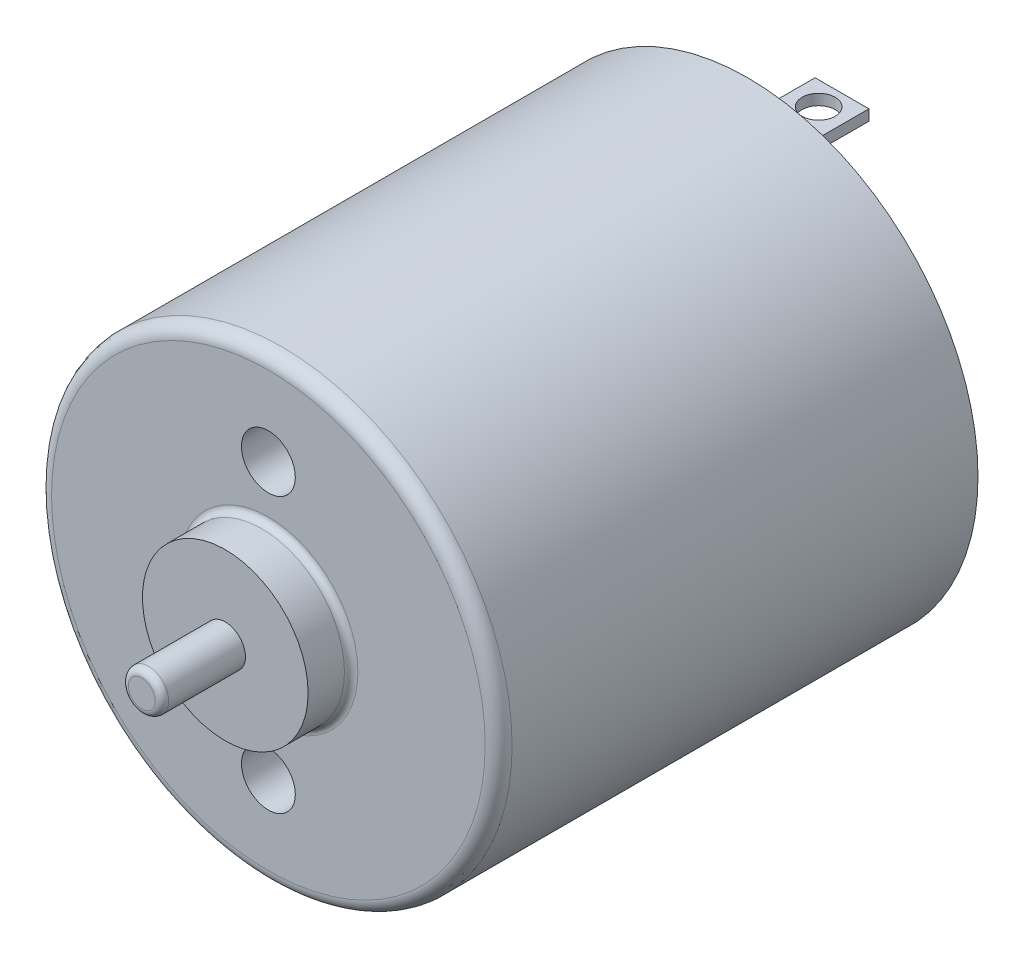
SolidWorks part; units mm, degrees
ref_plane "Front Plane" through (0, 0, 0) normal (0, 0, 1) x (1, 0, 0)
ref_plane "Top Plane" through (0, 0, 0) normal (0, 1, 0) x (1, 0, 0)
ref_plane "Right Plane" through (0, 0, 0) normal (1, 0, 0) x (0, 0, -1)
sketch "Sketch1" plane through (0, 0, 0) normal (0, 0, 1) x (1, 0, 0)
  circle A0 centre (0, 0) radius 8.55
  dimension "D1" = 17.1
extrude "Boss-Extrude1" add sketch "Sketch1" along normal blind 17.8
sketch "Sketch2" plane through (0, 0, 17.8) normal (0, 0, 1) x (1, 0, 0)
  circle A0 centre (0, 0) radius 3.075
  dimension "D1" = 6.15
extrude "Boss-Extrude2" add sketch "Sketch2" along normal blind 1.6
sketch "Sketch3" plane through (0, 0, 19.4) normal (0, 0, 1) x (1, 0, 0)
  circle A0 centre (0, 0) radius 0.75
  dimension "D1" = 1.5
extrude "Boss-Extrude3" add sketch "Sketch3" along normal offset from surface (3.1 mm away) 4.7 up to face at (3.075, 0, 17.8) offset beyond the face yes
sketch "Sketch4" plane through (0, 0, 17.8) normal (0, 0, 1) x (1, 0, 0)
  line L0 (0, 5.1) -> (0, -5.1) construction
  circle A0 centre (0, 5.1) radius 1
  circle A1 centre (0, -5.1) radius 1
  point P4 (0, 0)
  dimension "D2" = 2
  dimension "D1" = 10.2
extrude "Cut-Extrude1" cut sketch "Sketch4" against normal blind 2
sketch "Sketch5" plane through (0, 0, 0) normal (0, 0, -1) x (-1, 0, 0)
  circle A0 centre (0, 0) radius 2.35
  dimension "D1" = 4.7
extrude "Boss-Extrude4" add sketch "Sketch5" along normal blind 2.16
sketch "Sketch6" plane through (0, 0, 0) normal (0, 0, -1) x (-1, 0, 0)
  line L0 (0, 6.1) -> (0, -6.1) construction
  line L1 (-1, 5.9) -> (1, 5.9)
  line L2 (-1, 5.9) -> (-1, 6.3)
  line L3 (-1, 6.3) -> (1, 6.3)
  line L4 (1, 5.9) -> (1, 6.3)
  line L5 (-1, 5.9) -> (1, 6.3) construction
  line L6 (-1, 6.3) -> (1, 5.9) construction
  line L7 (-1, -6.3) -> (1, -6.3)
  line L8 (-1, -6.3) -> (-1, -5.9)
  line L9 (-1, -5.9) -> (1, -5.9)
  line L10 (1, -6.3) -> (1, -5.9)
  line L11 (-1, -6.3) -> (1, -5.9) construction
  line L12 (-1, -5.9) -> (1, -6.3) construction
  point P0 (0, 6.1)
  point P5 (0, -6.1)
  point P12 (0, 0)
  dimension "D1" = 11.8
  dimension "D2" = 2
  dimension "D3" = 0.4
  dimension "D4" = 0.4
extrude "Boss-Extrude5" add sketch "Sketch6" along normal blind 3.5
fillet "Fillet1" radius 0.5 1 edges at (8.55, 0, 17.8)
fillet "Fillet2" radius 0.25 1 edges at (3.075, 0, 17.8)
fillet "Fillet3" radius 0.5 1 edges at (-2.35, 0, -2.16)
sketch "Sketch7" plane through (0, 0, 0) normal (0, 0, -1) x (-1, 0, 0)
  line L0 (1, 5.9) -> (1, 6.3) construction
  line L1 (1, 6.3) -> (-1, 6.3) construction
  line L2 (-1, 6.3) -> (-1, 5.9) construction
  line L3 (-1, 5.9) -> (1, 5.9) construction
  line L4 (1, -6.3) -> (1, -5.9) construction
  line L5 (1, -5.9) -> (-1, -5.9) construction
  line L6 (-1, -5.9) -> (-1, -6.3) construction
  line L7 (-1, -6.3) -> (1, -6.3) construction
  line L8 (1, 5.9) -> (1, 6.3)
  line L9 (1, 6.3) -> (-1, 6.3)
  line L10 (-1, 6.3) -> (-1, 5.9)
  line L11 (-1, 5.9) -> (1, 5.9)
  line L12 (1, -6.3) -> (1, -5.9)
  line L13 (1, -5.9) -> (-1, -5.9)
  line L14 (-1, -5.9) -> (-1, -6.3)
  line L15 (-1, -6.3) -> (1, -6.3)
  circle A0 centre (0, 0) radius 2.35 construction
  circle A1 centre (0, 0) radius 8.55
  circle A2 centre (0, 0) radius 8.55 construction
  circle A3 centre (0, 0) radius 2.35
  circle A4 centre (0, 0) radius 8.3
  dimension "D1" = 0
  dimension "D2" = 0.25
extrude "Cut-Extrude2" cut sketch "Sketch7" against normal blind 0.5 contours A4
sketch "Sketch8" plane through (0, 6.3, 0) normal (0, 1, 0) x (1, 0, 0)
  circle A0 centre (0, 2.6329) radius 0.6132
extrude "Cut-Extrude3" cut sketch "Sketch8" against normal blind 15.5
fillet "Fillet4" radius 0.25 1 edges at (0.75, 0, 22.5)
equation "\"D1@Boss-Extrude4\"=19.96-17.8"
